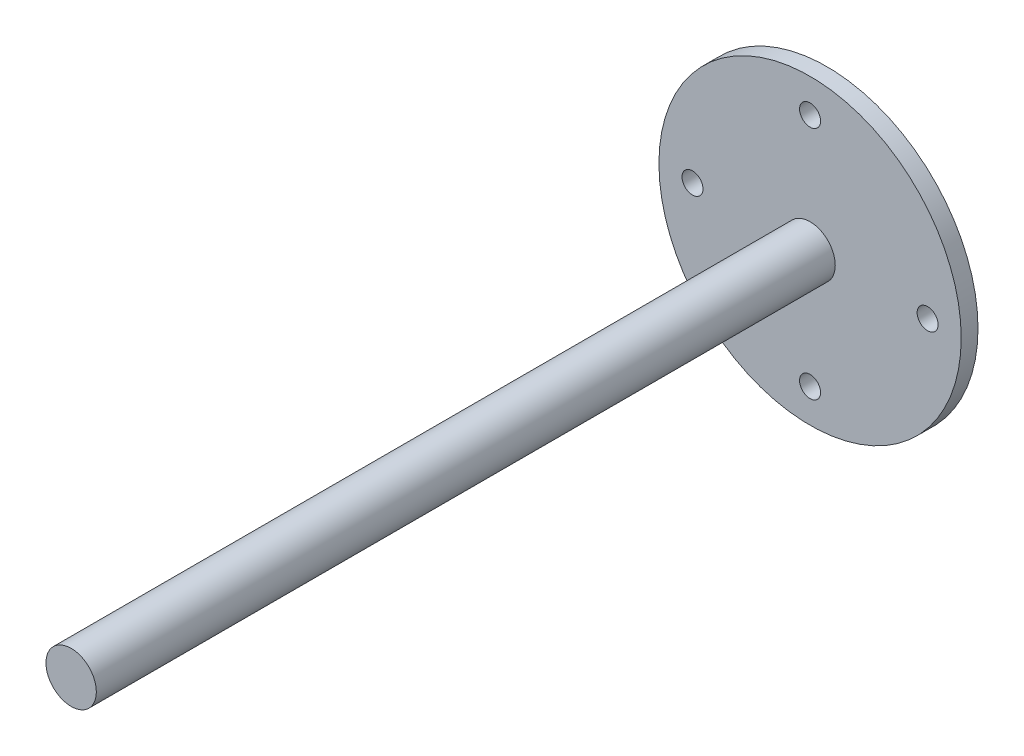
SolidWorks part; units mm, degrees
material "Plain Carbon Steel"
ref_plane "Front Plane" through (0, 0, 0) normal (0, 0, 1) x (1, 0, 0)
ref_plane "Top Plane" through (0, 0, 0) normal (0, 1, 0) x (1, 0, 0)
ref_plane "Right Plane" through (0, 0, 0) normal (1, 0, 0) x (0, 0, -1)
sketch "Sketch1" plane through (0, 0, 0) normal (0, 0, 1) x (1, 0, 0)
  circle A0 centre (0, 0) radius 57.15
  circle A1 centre (0, 44.45) radius 3.9688
  circle A2 centre (44.45, 0) radius 3.9687
  circle A3 centre (0, -44.45) radius 3.9688
  circle A4 centre (-44.45, 0) radius 3.9687
  point P5 (-53.7077, 0)
  point P14 (0, 0)
  dimension "D1" = 7.9375
  dimension "D3" = 114.3
  dimension "D2" = 44.45
  dimension "D4" = 4
extrude "Boss-Extrude1" add sketch "Sketch1" along normal blind 6.35
sketch "Sketch2" plane through (0, 0, 6.35) normal (0, 0, 1) x (1, 0, 0)
  circle A0 centre (0, 0) radius 9.525
  dimension "D1" = 19.05
extrude "Boss-Extrude2" add sketch "Sketch2" along normal blind 279.4
